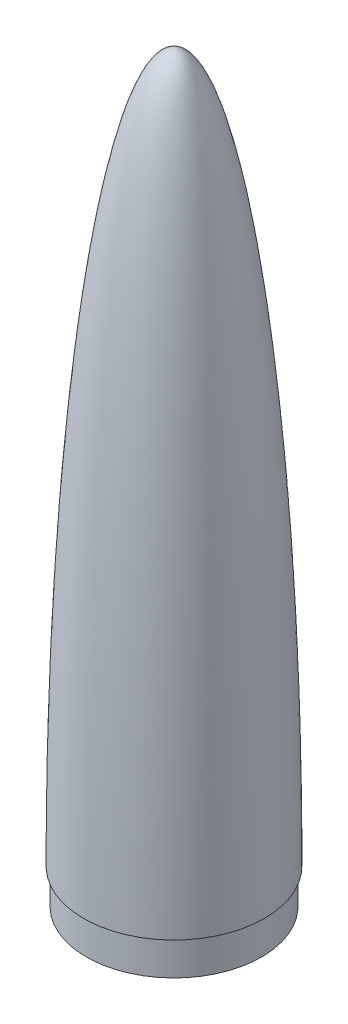
SolidWorks part; units mm, degrees
ref_plane "Alzado" through (0, 0, 0) normal (0, 0, 1) x (1, 0, 0)
ref_plane "Planta" through (0, 0, 0) normal (0, 1, 0) x (1, 0, 0)
ref_plane "Vista lateral" through (0, 0, 0) normal (1, 0, 0) x (0, 0, -1)
sketch "Croquis1" plane through (0, 0, 0) normal (0, 0, 1) x (1, 0, 0)
  line L0 (38.99, 0) -> (-38.99, 0) construction
  line L1 (0, 0) -> (0, 303.8)
  line L2 (38.99, 0) -> (37.79, 0)
  line L3 (0, 305) -> (0, 303.8)
  ellipse E0 centre (0, 0) end of major axis (0, 305) minor radius 38.99 (38.99, 0) -> (0, 305) ccw
  spline S0 degree 1 poles (37.79, 0) (0, 303.8) knots 0 0 1 1 construction
  spline S1 degree 3 poles (37.79, 0) (37.79, 9.9602) (37.6647, 29.9356) (37.1027, 59.5659) (36.1719, 88.6332) (34.4516, 126.2464) (31.432, 170.441) (26.5567, 216.9094) (21.6094, 248.6633) (17.2409, 269.1425) (13.7952, 281.8882) (10.2235, 291.881) (7.1916, 297.8074) (4.8016, 301.0427) (3.0714, 302.7055) (1.4484, 303.6198) (0.5034, 303.8) (0, 303.8) knots -1.570796 -1.570796 -1.570796 -1.570796 -1.472622 -1.374447 -1.276272 -1.178097 -0.981748 -0.785398 -0.589049 -0.490874 -0.392699 -0.294524 -0.19635 -0.147262 -0.098175 -0.049087 0 0 0 0
  point P4 (0, 0)
  dimension "D1" = 77.98
  dimension "D2" = 305
  dimension "D3" = 1.2
revolve "Revolución1" add sketch "Croquis1" angle 360 about L1
sketch "Sketch1" plane through (0, 0, 0) normal (0, 0, 1) x (1, 0, 0)
  line L0 (37.79, 0) -> (37.79, -15)
  line L1 (-38.99, 0) -> (38.99, 0) construction
  line L2 (-37.79, 0) -> (37.79, 0) construction
  line L3 (37.79, -15) -> (36.29, -15)
  line L4 (36.29, -15) -> (36.29, 0)
  line L6 (36.29, 0) -> (36.29, 1.5)
  line L8 (37.79, 1.5) -> (37.79, 0)
  line L9 (0, 0) -> (0, 27.4205) construction
  line L10 (37.79, 3) -> (37.79, 1.5)
  line L12 (37.79, 3) -> (36.29, 1.5)
  dimension "D1" = 15
  dimension "D2" = 1.5
  dimension "D3" = 1.5
  dimension "D4" = 37.79
  dimension "D5" = 3
  dimension "D6" = 1.5
revolve "Revolve1" add sketch "Sketch1" angle 360 about L9
sketch "Sketch2" plane through (0, 0, 0) normal (0, 0, 1) x (1, 0, 0)
  line L0 (-38.8, 0) -> (-38.8, 100) construction
  line L1 (-38.99, 0) -> (38.99, 0) construction
  line L2 (-37.79, 0) -> (37.79, 0) construction
  line L3 (0, 0) -> (0, 100) construction
  line L4 (0, 100) -> (36, 100) construction
  dimension "D1" = 100
  dimension "D2" = 36
sketch "Croquis3" plane through (0, 0, 0) normal (0, 0, 1) x (1, 0, 0)
  line L0 (36.2855, 1.5) -> (31.2881, 1.5)
  line L1 (36.29, 1.5) -> (-36.29, 1.5) construction
  line L2 (31.2881, 1.5) -> (31.2881, 2.9981)
  line L3 (37.7881, 2.9981) -> (-37.7881, 2.9981) construction
  line L4 (31.2881, 2.9981) -> (37.7881, 2.9981)
  line L5 (37.7881, 2.9981) -> (36.2855, 1.5)
  line L6 (0, 0) -> (0, -27.6563) construction
  point P11 (37.7881, 2.9981)
  point P12 (36.2855, 1.5)
  dimension "D1" = 6.5
revolve "Revolución2" add sketch "Croquis3" angle 360 about L6
sketch "Croquis4" plane through (0, 1.5, 0) normal (0, -1, 0) x (1, 0, 0)
  line L0 (0, 0) -> (0, 30) construction
  line L1 (14, 30) -> (-14, 30) construction
  line L2 (0, 0) -> (-36.2855, 0) construction
  circle A0 centre (-14, 30) radius 1.6
  circle A1 centre (14, 30) radius 1.6
  circle A2 centre (0, 0) radius 36.2855 construction
  circle A3 centre (14, -30) radius 1.6
  circle A4 centre (-14, -30) radius 1.6
  point P6 (0, 30)
  dimension "D3" = 3.2
  dimension "D4" = 3.2
  dimension "D1" = 30
  dimension "D2" = 28
extrude "Cortar-Extruir1" cut sketch "Croquis4" against normal blind 10
